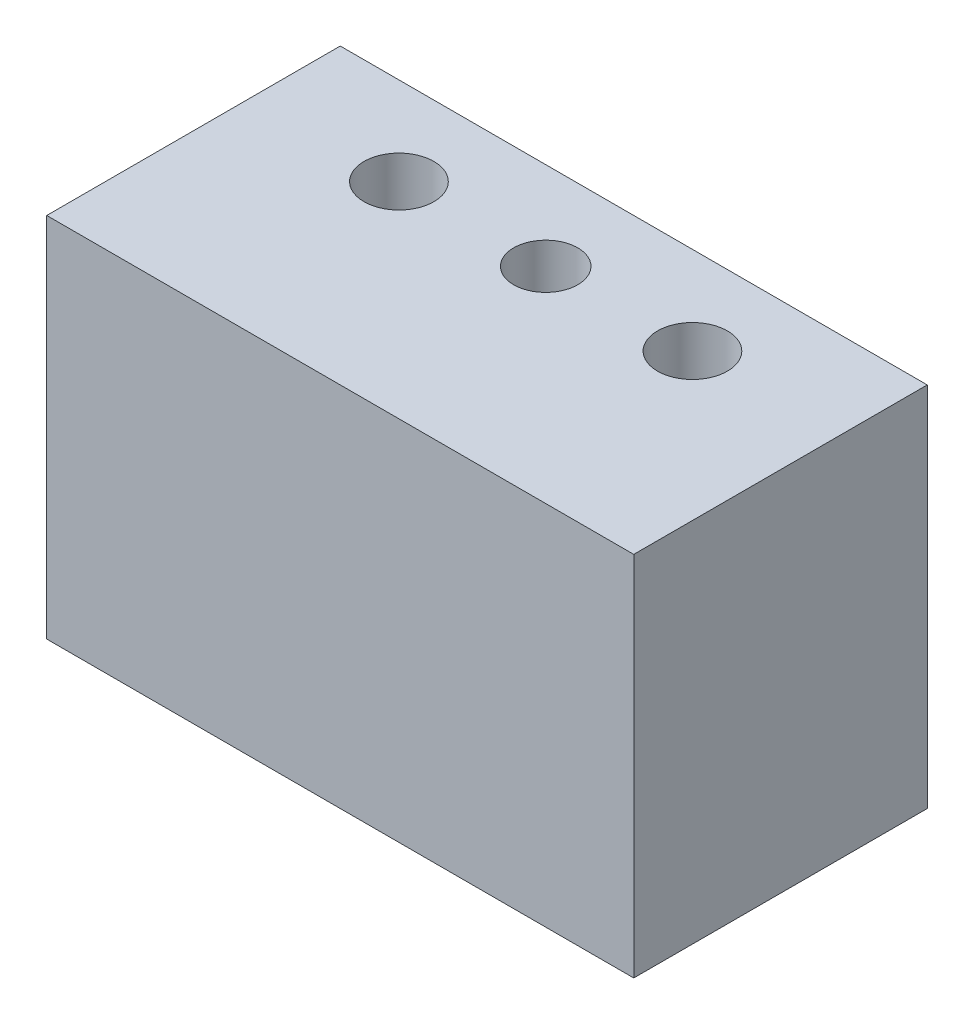
SolidWorks part; units mm, degrees
ref_plane "Front" through (0, 0, 0) normal (0, 0, 1) x (1, 0, 0)
ref_plane "Top" through (0, 0, 0) normal (0, 1, 0) x (1, 0, 0)
ref_plane "Right" through (0, 0, 0) normal (1, 0, 0) x (0, 0, -1)
sketch "Sketch1" plane through (0, 0, 0) normal (0, 1, 0) x (1, 0, 0)
  line L1 (0, 0) -> (40, 0)
  line L2 (0, 0) -> (0, 20)
  line L3 (0, 20) -> (40, 20)
  line L4 (40, 0) -> (40, 20)
  circle A0 centre (10, 14) radius 2.38
  circle A1 centre (30, 14) radius 2.38
  dimension "D1" = 6
  dimension "D2" = 20
  dimension "D3" = 10
extrude "Boss-Extrude1" add sketch "Sketch1" along normal blind 25
hole_wizard "11/64 (0.17188) Diameter Hole1" positions "Sketch3" profile "Sketch2" hole size "11/64" standard "ANSI Inch" end condition through all
sketch "Sketch3" plane through (0, 25, 0) normal (0, 1, 0) x (1, 0, 0)
  line L0 (0, 20) -> (0, 0) construction
  line L1 (40, 20) -> (0, 20) construction
  point P0 (20, 14)
  dimension "D1" = 20
  dimension "D2" = 6
sketch "Sketch2" plane through (20, 25, -14) normal (1, 0, 0) x (0, 0, 1)
  line L0 (0, 0) -> (0, 25)
  line L1 (0, 25) -> (2.1829, 25)
  line L2 (2.1829, 25) -> (2.1829, 0)
  line L5 (2.1829, 0) -> (0, 0)
  line L11 (0, -6.35) -> (0, 107.95) construction
  dimension "Thru Hole Dia." = 4.3658
  dimension "Thru Hole Depth" = 25
